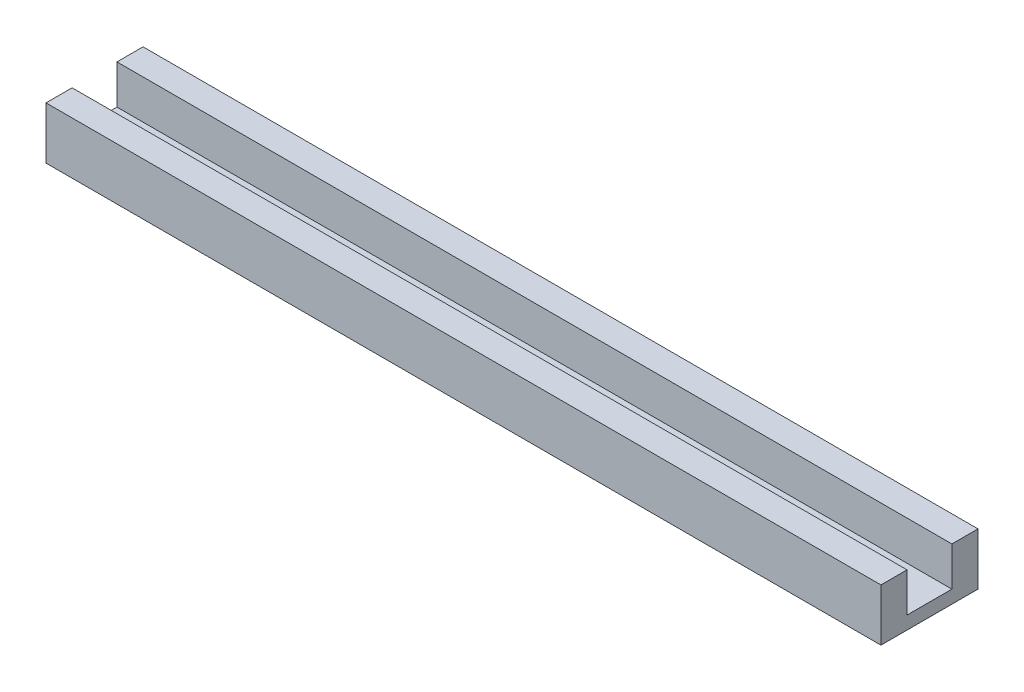
SolidWorks part; units mm, degrees
ref_plane "Front Plane" through (0, 0, 0) normal (0, 0, 1) x (1, 0, 0)
ref_plane "Top Plane" through (0, 0, 0) normal (0, 1, 0) x (1, 0, 0)
ref_plane "Right Plane" through (0, 0, 0) normal (1, 0, 0) x (0, 0, -1)
sketch "Sketch2" plane through (0, 0, 0) normal (0, 1, 0) x (1, 0, 0)
  line L1 (-15.7347, 12.6633) -> (187.4653, 12.6633)
  line L2 (-15.7347, 12.6633) -> (-15.7347, -10.9587)
  line L3 (-15.7347, -10.9587) -> (187.4653, -10.9587)
  line L4 (187.4653, 12.6633) -> (187.4653, -10.9587)
  dimension "D1" = 23.622
  dimension "D2" = 203.2
extrude "Boss-Extrude2" add sketch "Sketch2" along normal blind 3.175
sketch "Sketch3" plane through (0, 3.175, 0) normal (0, 1, 0) x (1, 0, 0)
  line L0 (187.4653, -10.9587) -> (187.4653, 12.6633) construction
  line L1 (-15.7347, 12.6633) -> (187.4653, 12.6633)
  line L2 (-15.7347, 12.6633) -> (-15.7347, 6.3133)
  line L3 (-15.7347, 6.3133) -> (187.4653, 6.3133)
  line L4 (187.4653, 12.6633) -> (187.4653, 6.3133)
  line L5 (-15.7347, 12.6633) -> (-15.7347, -10.9587) construction
  line L6 (187.4653, -10.9587) -> (-15.7347, -10.9587)
  line L7 (187.4653, -10.9587) -> (187.4653, -4.6087)
  line L8 (187.4653, -4.6087) -> (-15.7347, -4.6087)
  line L9 (-15.7347, -10.9587) -> (-15.7347, -4.6087)
  dimension "D1" = 6.35
  dimension "D2" = 6.35
extrude "Boss-Extrude3" add sketch "Sketch3" along normal blind 9.525
